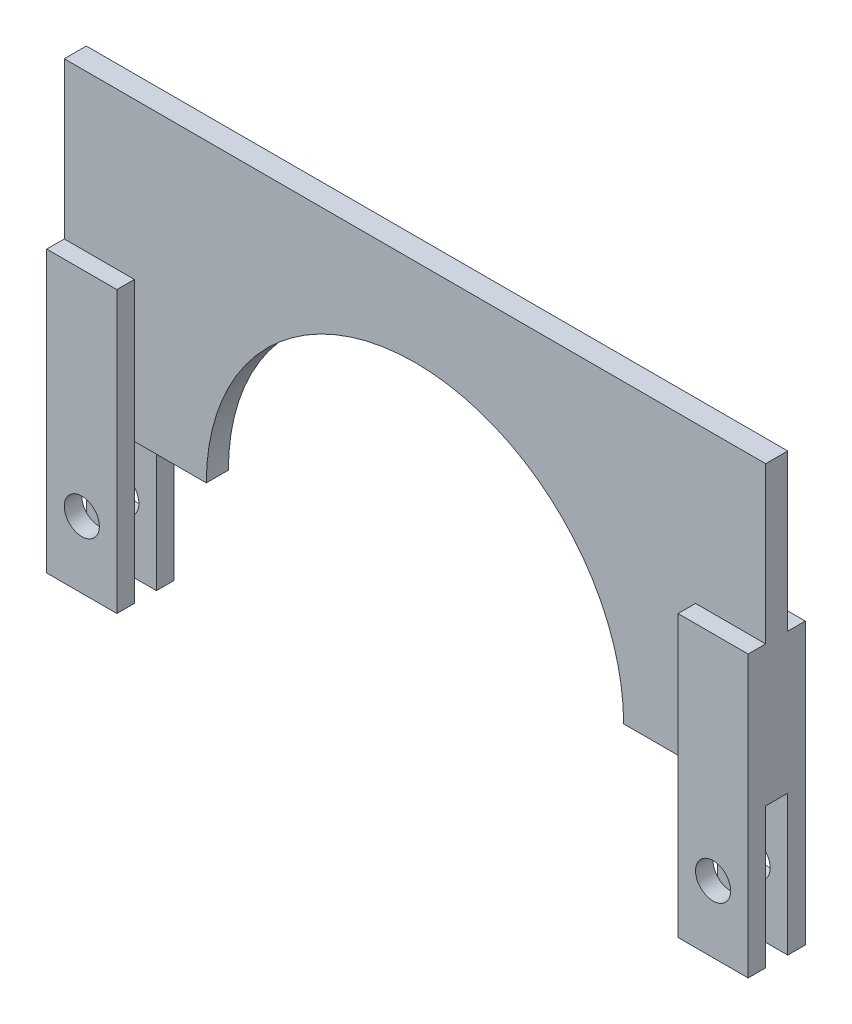
SolidWorks part; units mm, degrees
ref_plane "Front Plane" through (0, 0, 0) normal (0, 0, 1) x (1, 0, 0)
ref_plane "Top Plane" through (0, 0, 0) normal (0, 1, 0) x (1, 0, 0)
ref_plane "Right Plane" through (0, 0, 0) normal (1, 0, 0) x (0, 0, -1)
sketch "Sketch1" plane through (0, 0, 0) normal (0, 0, 1) x (1, 0, 0)
  line L0 (-25.4, 0) -> (-15.113, 0)
  line L1 (15.113, 0) -> (25.4, 0)
  line L2 (-25.4, 0) -> (-25.4, 21.463)
  line L3 (-25.4, 21.463) -> (25.4, 21.463)
  line L4 (25.4, 21.463) -> (25.4, 0)
  line L5 (0, 0) -> (7.308, 0) construction
  arc A0 (15.113, 0) -> (-15.113, 0) centre (0, 0) ccw
  point P4 (0, 15.113)
  point P7 (0, 0)
  dimension "D1" = 15.113
  dimension "D2" = 50.8
  dimension "D3" = 6.35
extrude "Boss-Extrude1" add sketch "Sketch1" along normal mid plane 1.5971
sketch "Sketch2" plane through (0, 0, 0.7986) normal (0, 0, 1) x (1, 0, 0)
  line L0 (25.4, 0) -> (20.32, 0)
  line L1 (15.113, 0) -> (25.4, 0) construction
  line L2 (25.4, 0) -> (25.4, -10.16)
  line L3 (25.4, -10.16) -> (20.32, -10.16)
  line L4 (20.32, -10.16) -> (20.32, 0)
  line L5 (20.32, 0) -> (20.32, 10.16)
  line L6 (20.32, 10.16) -> (25.4, 10.16)
  line L7 (25.4, 0) -> (25.4, 21.463) construction
  line L8 (25.4, 10.16) -> (25.4, 0)
  point P7 (0, 0)
  line M7 (15.113, 0) -> (25.4, 0)
  line M8 (25.4, 0) -> (25.4, 21.463)
  dimension "D1" = 5.08
  dimension "D2" = 10.16
extrude "Boss-Extrude3" add sketch "Sketch2" along normal blind 1.27 contours L6 L5 M7 M8 | L4 L3 L2 M7
mirror "Mirror1" about plane through (0, 0, 0) normal (0, 0, 1) of "Boss-Extrude3"
mirror "Mirror2" about plane through (0, 0, 0) normal (1, 0, 0) of "Mirror1", "Boss-Extrude3"
sketch "Sketch3" plane through (0, 0, -2.0686) normal (0, 0, -1) x (-1, 0, 0)
  line L0 (-25.4, 0) -> (-22.86, 0) construction
  line L1 (-25.4, -10.16) -> (-25.4, 10.16) construction
  line L2 (-25.4, 0) -> (-25.4, -5.334)
  circle A0 centre (-22.86, -5.334) radius 1.27
  dimension "D3" = 2.54
  dimension "D1" = 2.54
  dimension "D2" = 5.334
extrude "Cut-Extrude1" cut sketch "Sketch3" against normal through all contours A0
mirror "Mirror3" about plane through (0, 0, 0) normal (1, 0, 0) of "Cut-Extrude1"
